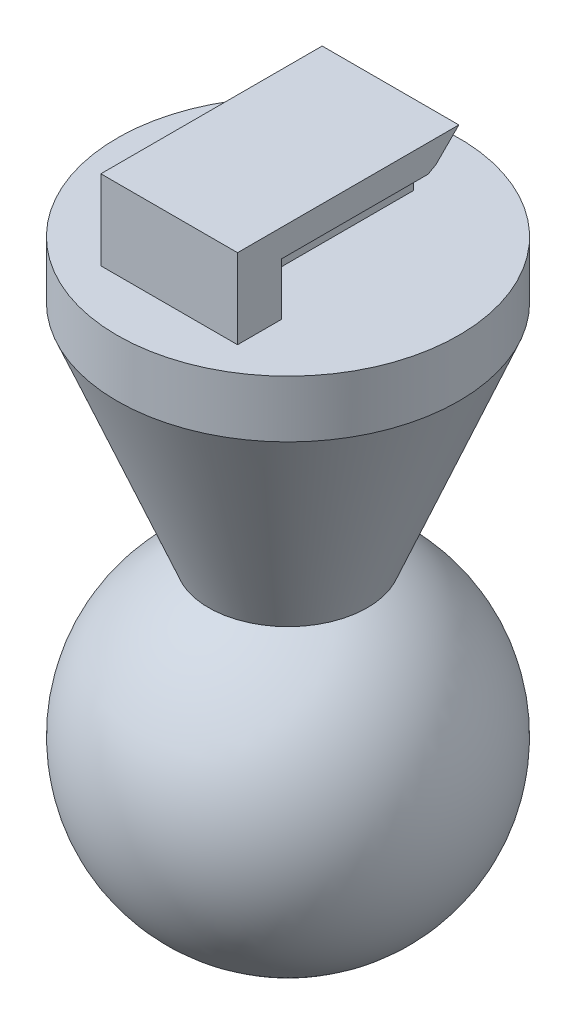
SolidWorks part; units mm, degrees
ref_plane "Alzado" through (0, 0, 0) normal (0, 0, 1) x (1, 0, 0)
ref_plane "Planta" through (0, 0, 0) normal (0, 1, 0) x (1, 0, 0)
ref_plane "Vista lateral" through (0, 0, 0) normal (1, 0, 0) x (0, 0, -1)
sketch "Croquis1" plane through (0, 0, 0) normal (1, 0, 0) x (0, 0, -1)
  line L0 (0, 0) -> (0, 4)
  line L1 (0, 4) -> (9, 4)
  line L2 (9, 4) -> (8, 3)
  line L3 (8, 3) -> (1, 3)
  line L4 (1, 3) -> (1, 0)
  line L5 (1, 0) -> (0, 0)
  dimension "D1" = 1
  dimension "D2" = 1
  dimension "D3" = 45
  dimension "D4" = 4
  dimension "D5" = 9
extrude "Saliente-Extruir1" add sketch "Croquis1" along normal mid plane 6
sketch "Croquis2" plane through (0, 0, 0) normal (1, 0, 0) x (0, 0, -1)
  line L1 (9, 4) -> (0, 4)
  line L2 (9, 4) -> (9, 0)
  line L3 (9, 0) -> (0, 0)
  line L4 (0, 4) -> (0, 0)
extrude "Saliente-Extruir2" add sketch "Croquis2" along normal mid plane 2
sketch "Croquis3" plane through (0, 0, 0) normal (0, -1, 0) x (1, 0, 0)
  line L0 (0, 0) -> (0, -9) construction
  line L1 (1, -9) -> (-1, -9) construction
  line L2 (0, -4.5) -> (3, -4.5) construction
  line L3 (3, -1) -> (3, -8) construction
  circle A0 centre (0, -4.5) radius 7.5
  dimension "D1" = 15
extrude "Saliente-Extruir3" add sketch "Croquis3" along normal blind 2
sketch "Croquis4" plane through (0, 0, 0) normal (1, 0, 0) x (0, 0, -1)
  line L0 (-3, -2) -> (1.4754, -13)
  line L1 (1.4754, -13) -> (4.5, -13)
  line L2 (4.5, -13) -> (4.5, -2)
  line L3 (-3, -2) -> (12, -2) construction
  line L4 (4.5, -2) -> (-3, -2)
  dimension "D1" = 11
revolve "Revolución1" add sketch "Croquis4" angle 360 about L2
sketch "Croquis5" plane through (0, 0, 0) normal (1, 0, 0) x (0, 0, -1)
  line L0 (4.5, 0) -> (4.5, -20.3293) construction
  line L1 (12, 0) -> (-3, 0) construction
  line L3 (4.5, -26) -> (-7.5012, -26) construction
  line L5 (4.5, -11) -> (-11.6499, -11) construction
  line L6 (4.5, -11) -> (4.5, -26)
  arc A0 (4.5, -11) -> (4.5, -26) centre (4.5, -18.5) ccw
  dimension "D1" = 15
  dimension "D2" = 11
revolve "Revolución2" add sketch "Croquis5" angle 360 about L6
sketch "Croquis6" plane through (0, 0, 0) normal (1, 0, 0) x (0, 0, -1)
  line L0 (4.5, 0) -> (4.5, -27.489) construction
  line L1 (12, 0) -> (-3, 0) construction
  line L2 (11.0377, -13.1723) -> (14.9272, -13.1723)
  line L3 (-5.9272, -32.6199) -> (14.9272, -32.6199)
  line L4 (-5.9272, -32.6199) -> (-5.9272, -13.1723)
  line L5 (-5.9272, -13.1723) -> (-2.0377, -13.1723)
  line L6 (14.9272, -32.6199) -> (14.9272, -13.1723)
  line L7 (-5.9272, -32.6199) -> (14.9272, -13.1723) construction
  line L8 (-5.9272, -13.1723) -> (14.9272, -32.6199) construction
  line L10 (-2.0377, -13.1723) -> (-2.0377, -24.4685)
  line L11 (-2.0377, -24.4685) -> (11.0377, -24.4685)
  line L12 (11.0377, -13.1723) -> (11.0377, -24.4685)
  line L13 (5.5796, -13.1723) -> (11.0377, -24.4685) construction
  line L14 (-2.0377, -24.4685) -> (3.4204, -13.1723) construction
  point P4 (4.5, -22.8961)
  point P9 (4.5, -10.9379)
sketch "Croquis7" plane through (0, 0, 0) normal (1, 0, 0) x (0, 0, -1)
  line L0 (1, 3) -> (1, 0) construction
  line L1 (1, 3) -> (8, 3) construction
  line L2 (1, 3) -> (1, 0)
  line L3 (1, 3) -> (8, 3)
  line L4 (8, 3) -> (7.6531, 2.8)
  line L5 (7.6531, 2.8) -> (1.2045, 2.8)
  line L6 (1.2045, 2.8) -> (1.2045, 0)
  line L7 (1, 0) -> (9, 0) construction
  line L8 (1.2045, 0) -> (1, 0)
  line L9 (0, 4) -> (-0.7149, 4)
  line L10 (-0.7149, 4) -> (-0.7149, 0)
  line L11 (12, 0) -> (-3, 0) construction
  line L12 (-0.7149, 0) -> (0, 0)
  line L13 (0, 0) -> (0, 4)
  dimension "D1" = 0.2
  dimension "D2" = 0.2045
extrude "Saliente-Extruir4" add sketch "Croquis7" along normal up to surface and the other way up to vertex
sketch "Croquis8" plane through (0, 0, 0) normal (0, 1, 0) x (1, 0, 0)
  circle A1 centre (0, 4.5) radius 7.5
  circle A2 centre (0, 4.5) radius 7.5
  dimension "D1" = 0
extrude "Saliente-Extruir5" add sketch "Croquis8" along normal blind 0.5
